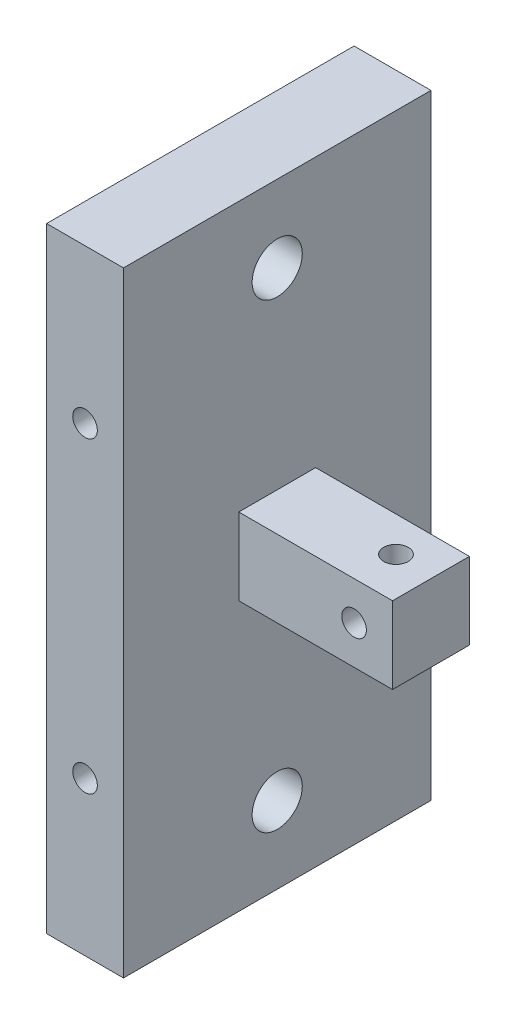
SolidWorks part; units mm, degrees
ref_plane "Front Plane" through (0, 0, 0) normal (0, 0, 1) x (1, 0, 0)
ref_plane "Top Plane" through (0, 0, 0) normal (0, 1, 0) x (1, 0, 0)
ref_plane "Right Plane" through (0, 0, 0) normal (1, 0, 0) x (0, 0, -1)
sketch "Sketch1" plane through (0, 0, 0) normal (1, 0, 0) x (0, 0, -1)
  line L1 (-1106.087, 761.7391) -> (-1066.087, 761.7391)
  line L2 (-1106.087, 761.7391) -> (-1106.087, 681.7391)
  line L3 (-1106.087, 681.7391) -> (-1066.087, 681.7391)
  line L4 (-1066.087, 761.7391) -> (-1066.087, 681.7391)
  dimension "D1" = 80
  dimension "D2" = 40
extrude "Boss-Extrude1" add sketch "Sketch1" along normal blind 10
sketch "Sketch2" plane through (10, 0, 0) normal (1, 0, 0) x (0, 0, -1)
  line L0 (-1066.087, 761.7391) -> (-1106.087, 761.7391) construction
  line L1 (-1091.087, 726.7391) -> (-1081.087, 726.7391)
  line L2 (-1091.087, 726.7391) -> (-1091.087, 716.7391)
  line L3 (-1091.087, 716.7391) -> (-1081.087, 716.7391)
  line L4 (-1081.087, 726.7391) -> (-1081.087, 716.7391)
  line L6 (-1066.087, 681.7391) -> (-1066.087, 761.7391) construction
  dimension "D1" = 35
  dimension "D2" = 10
  dimension "D3" = 10
  dimension "D4" = 15
extrude "Boss-Extrude2" add sketch "Sketch2" along normal blind 20
hole_wizard "1/4 Clearance Hole1" positions "3DSketch3" profile "Sketch6" hole size "1/4" standard "ANSI Inch"
sketch3d "3DSketch3"
  line L0 (10, 681.7391, 1106.087) -> (10, 681.7391, 1066.087) construction
  line L1 (10, 681.7391, 1066.087) -> (10, 761.7391, 1066.087) construction
  line L2 (10, 761.7391, 1066.087) -> (10, 761.7391, 1106.087) construction
  point P0 (10, 751.7391, 1086.087)
  point P2 (10, 691.7391, 1086.087)
  dimension "D1" = 10
  dimension "D2" = 20
  dimension "D3" = 20
  dimension "D4" = 10
sketch "Sketch6" plane through (10, 751.7391, 1086.087) normal (0, 1, 0) x (0, 0, -1)
  line L0 (0, 0) -> (0, 22.9611)
  line L1 (0, 22.9611) -> (3.2639, 21)
  line L2 (3.2639, 21) -> (3.2639, 0)
  line L5 (3.2639, 0) -> (0, 0)
  line L10 (0, 22.9611) -> (-3.2639, 21) construction
  line L11 (0, -6.35) -> (0, 107.95) construction
  dimension "Hole Dia." = 6.5278
  dimension "Hole Depth" = 21
  dimension "Drill Angle" = 118
hole_wizard "M3 Clearance Hole3" positions "3DSketch5" profile "Sketch8" hole size "M3" standard "ANSI Metric" end condition through all
sketch3d "3DSketch5"
  line L0 (0, 681.7391, 1066.087) -> (0, 761.7391, 1066.087) construction
  line L1 (10, 681.7391, 1066.087) -> (0, 681.7391, 1066.087) construction
  line L2 (10, 761.7391, 1066.087) -> (0, 761.7391, 1066.087) construction
  point P0 (5, 701.7391, 1066.087)
  point P2 (5, 741.7391, 1066.087)
  dimension "D1" = 5
  dimension "D2" = 5
  dimension "D3" = 20
  dimension "D4" = 20
sketch "Sketch8" plane through (5, 701.7391, 1066.087) normal (1, 0, 0) x (0, 1, 0)
  line L0 (0, 0) -> (0, 40)
  line L1 (0, 40) -> (1.6, 40)
  line L2 (1.6, 40) -> (1.6, 0)
  line L5 (1.6, 0) -> (0, 0)
  line L11 (0, -6.35) -> (0, 107.95) construction
  dimension "Thru Hole Dia." = 3.2
  dimension "Thru Hole Depth" = 40
hole_wizard "M3 Clearance Hole4" positions "3DSketch6" profile "Sketch9" hole size "M3" standard "ANSI Metric" end condition through all
sketch3d "3DSketch6"
  line L0 (30, 726.7391, 1081.087) -> (30, 726.7391, 1091.087) construction
  line L1 (30, 726.7391, 1091.087) -> (10, 726.7391, 1091.087) construction
  line L2 (30, 716.7391, 1081.087) -> (30, 726.7391, 1081.087) construction
  line L3 (30, 716.7391, 1081.087) -> (10, 716.7391, 1081.087) construction
  point P0 (25, 726.7391, 1085.6397)
  point P5 (25, 721.7391, 1081.087)
  point P10 (0, 0, 0)
  dimension "D1" = 5
  dimension "D2" = 5.4472
  dimension "D3" = 5
  dimension "D4" = 5
sketch "Sketch9" plane through (25, 726.7391, 1085.6397) normal (1, 0, 0) x (0, 0, 1)
  line L0 (0, 0) -> (0, 45)
  line L1 (0, 45) -> (1.6, 45)
  line L2 (1.6, 45) -> (1.6, 0)
  line L5 (1.6, 0) -> (0, 0)
  line L11 (0, -6.35) -> (0, 107.95) construction
  dimension "Thru Hole Dia." = 3.2
  dimension "Thru Hole Depth" = 45
